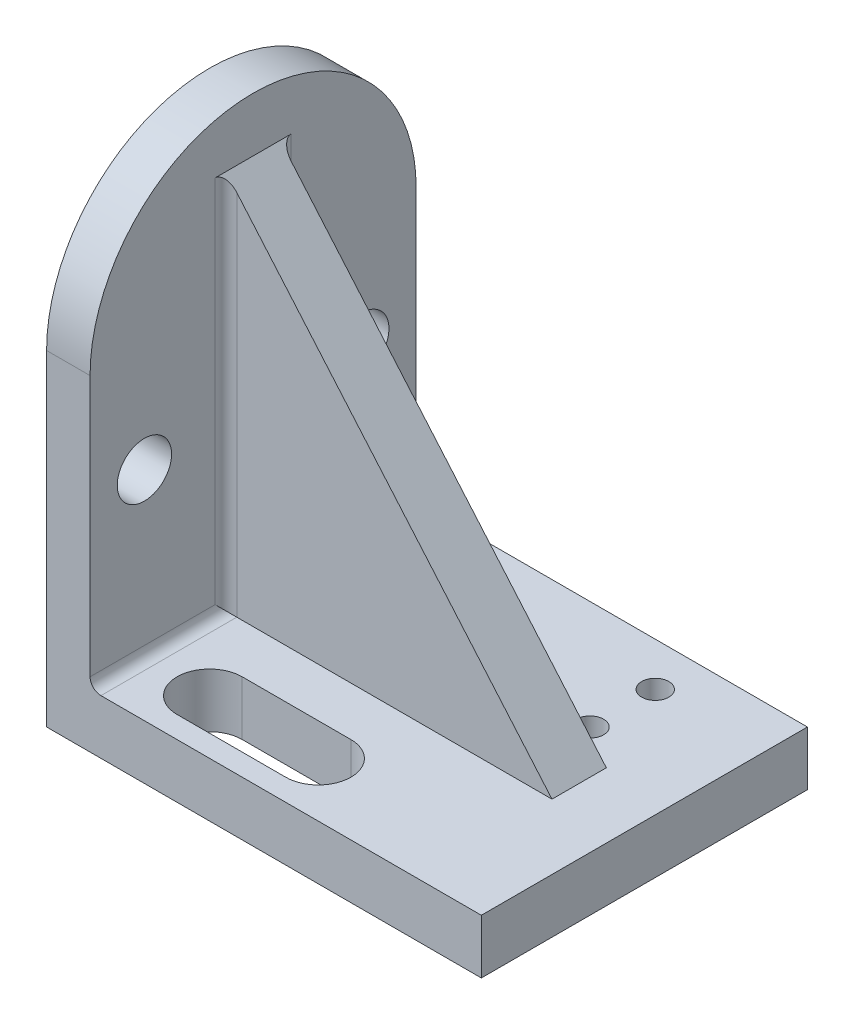
SolidWorks part; units mm, degrees
ref_plane "Front Plane" through (0, 0, 0) normal (0, 0, 1) x (1, 0, 0)
ref_plane "Top Plane" through (0, 0, 0) normal (0, 1, 0) x (1, 0, 0)
ref_plane "Right Plane" through (0, 0, 0) normal (1, 0, 0) x (0, 0, -1)
sketch "Sketch1" plane through (0, 0, 0) normal (0, 1, 0) x (1, 0, 0)
  line L1 (50.8, -38.1) -> (-50.8, -38.1)
  line L2 (50.8, -38.1) -> (50.8, 38.1)
  line L3 (50.8, 38.1) -> (-50.8, 38.1)
  line L4 (-50.8, -38.1) -> (-50.8, 38.1)
  line L5 (50.8, -38.1) -> (-50.8, 38.1) construction
  line L6 (50.8, 38.1) -> (-50.8, -38.1) construction
  point P0 (0, 0)
  dimension "D1" = 101.6
  dimension "D2" = 76.2
extrude "Boss-Extrude4" add sketch "Sketch1" along normal blind 12.7
sketch "Sketch4" plane through (-50.8, 0, 0) normal (-1, 0, 0) x (0, 0, 1)
  line L0 (38.1, 0) -> (38.1, 76.2)
  line L1 (-38.1, 0) -> (-38.1, 76.2)
  line L2 (-38.1, 0) -> (38.1, 0)
  arc A0 (-38.1, 76.2) -> (38.1, 76.2) centre (0, 76.2) cw
  dimension "D1" = 76.2
extrude "Boss-Extrude5" add sketch "Sketch4" against normal blind 10.16 contours L0 A0 L1 L2
sketch "Sketch5" plane through (0, 12.7, 0) normal (0, 1, 0) x (1, 0, 0)
  line L0 (-25.4, -25.4) -> (0, -25.4) construction
  line L1 (-25.4, -17.78) -> (0, -17.78)
  line L2 (-25.4, -33.02) -> (0, -33.02)
  line L3 (-50.8, 38.1) -> (-50.8, -38.1) construction
  line L4 (-40.64, -38.1) -> (50.8, -38.1) construction
  line L5 (50.8, 38.1) -> (-40.64, 38.1) construction
  arc A0 (-25.4, -17.78) -> (-25.4, -33.02) centre (-25.4, -25.4) ccw
  arc A1 (0, -33.02) -> (0, -17.78) centre (0, -25.4) ccw
  circle A2 centre (-25.4, 27.94) radius 3.175
  circle A3 centre (25.4, 27.94) radius 3.175
  circle A4 centre (25.4, 12.7) radius 3.175
  circle A5 centre (-25.4, 12.7) radius 3.175
  point P2 (-12.7, -25.4)
  point P15 (-23.3245, 12.842)
  dimension "D2" = 7.62
  dimension "D7" = 6.35
  dimension "D1" = 25.4
  dimension "D3" = 25.4
  dimension "D4" = 12.7
  dimension "D5" = 25.4
  dimension "D6" = 10.16
  dimension "D8" = 15.24
  dimension "D9" = 50.8
sketch "Sketch6" plane through (-40.64, 0, 0) normal (1, 0, 0) x (0, 0, -1)
  line L0 (-38.1, 0) -> (38.1, 0) construction
  line L1 (0, 55.88) -> (0, -55.88) construction
  circle A0 centre (-25.4, 50.8) radius 6.35
  circle A3 centre (25.4, 50.8) radius 6.35
  dimension "D1" = 12.7
  dimension "D3" = 50.8
  dimension "D2" = 50.8
extrude "Cut-Extrude1" cut sketch "Sketch5" against normal through all contours A1 L1 A0 L2
extrude "Cut-Extrude2" cut sketch "Sketch6" against normal through all
sketch "Sketch7" plane through (0, 0, 0) normal (0, 0, 1) x (1, 0, 0)
  line L0 (-40.64, 101.6) -> (35.56, 12.7)
  line L1 (-40.64, 76.2) -> (-40.64, 114.3) construction
  line L2 (-40.64, 12.7) -> (50.8, 12.7) construction
  dimension "D1" = 88.9
  dimension "D2" = 76.2
rib "Rib1" sketch "Sketch7" sketch "Sketch7" thickness 12.7 extrusion direction parallel to sketch draft on no parameters "D1"=12.7
fillet "Fillet2" radius 2.54 4 edges at (-40.64, 57.15, -6.35) (-40.64, 12.7, -22.225) (-40.64, 57.15, 6.35) (-40.64, 12.7, 22.225)
